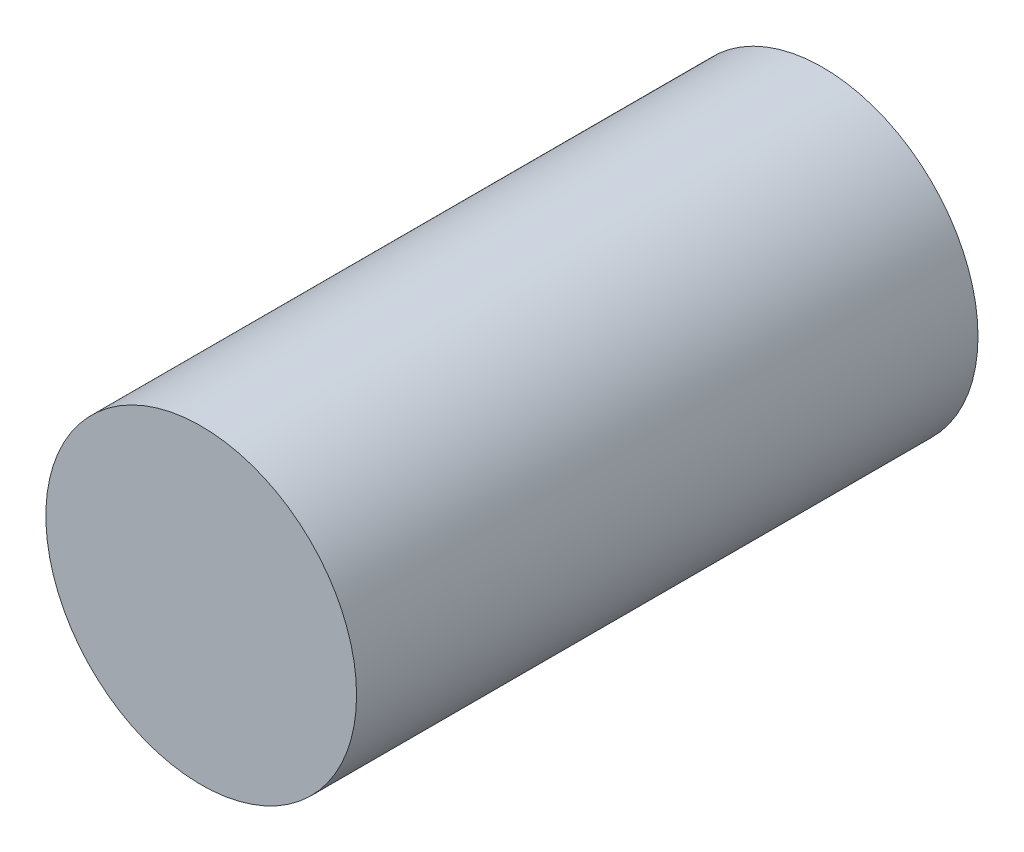
SolidWorks part; units mm, degrees
ref_plane "Front Plane" through (0, 0, 0) normal (0, 0, 1) x (1, 0, 0)
ref_plane "Top Plane" through (0, 0, 0) normal (0, 1, 0) x (1, 0, 0)
ref_plane "Right Plane" through (0, 0, 0) normal (1, 0, 0) x (0, 0, -1)
sketch "Sketch1" plane through (0, 0, 0) normal (0, 0, 1) x (1, 0, 0)
  circle A0 centre (0, 0) radius 1.25
  dimension "D1" = 2.5
extrude "Boss-Extrude1" add sketch "Sketch1" along normal blind 5
